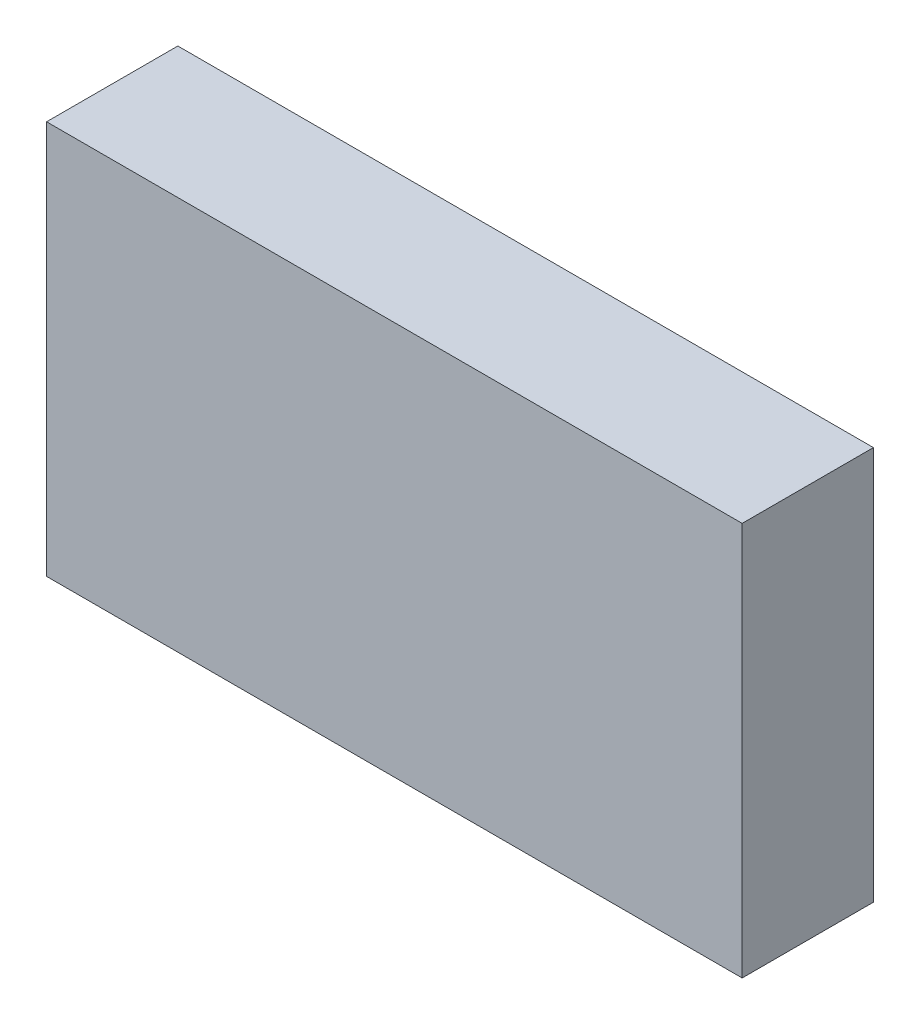
SolidWorks part; units mm, degrees
ref_plane "Alzado" through (0, 0, 0) normal (0, 0, 1) x (1, 0, 0)
ref_plane "Planta" through (0, 0, 0) normal (0, 1, 0) x (1, 0, 0)
ref_plane "Vista lateral" through (0, 0, 0) normal (1, 0, 0) x (0, 0, -1)
sketch "Croquis1" plane through (0, 0, 0) normal (0, 0, 1) x (1, 0, 0)
  line L1 (-26.5, 15) -> (26.5, 15)
  line L2 (-26.5, 15) -> (-26.5, -15)
  line L3 (-26.5, -15) -> (26.5, -15)
  line L4 (26.5, 15) -> (26.5, -15)
  line L5 (-26.5, 15) -> (26.5, -15) construction
  line L6 (-26.5, -15) -> (26.5, 15) construction
  point P0 (0, 0)
  dimension "D1" = 53
  dimension "D2" = 30
extrude "Saliente-Extruir1" add sketch "Croquis1" along normal blind 10
